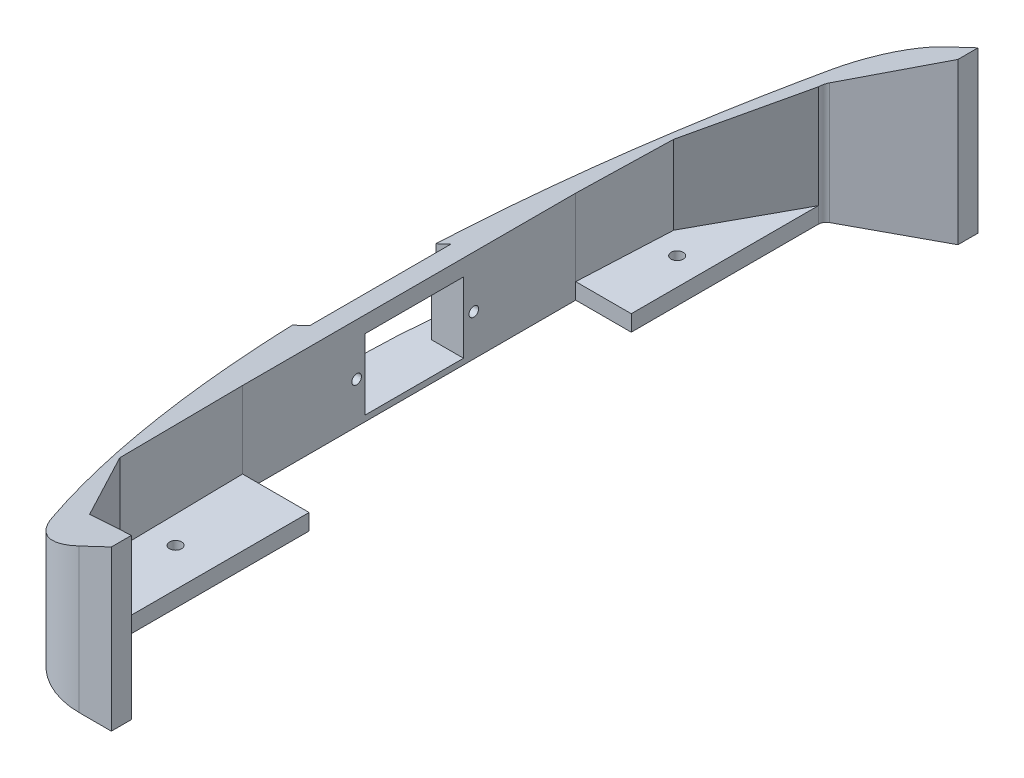
SolidWorks part; units mm, degrees
ref_plane "Front Plane" through (0, 0, 0) normal (0, 0, 1) x (1, 0, 0)
ref_plane "Top Plane" through (0, 0, 0) normal (0, 1, 0) x (1, 0, 0)
ref_plane "Right Plane" through (0, 0, 0) normal (1, 0, 0) x (0, 0, -1)
sketch "front_sketch" plane through (0, 0, 0) normal (0, 1, 0) x (1, 0, 0)
  line L4 (-94.9614, 124.4785) -> (-121.3453, 110.2345)
  line L10 (-122.6787, 107.9994) -> (-122.6787, 48.8108)
  line L24 (-94.9614, 130.8285) -> (-94.9614, 124.4785) construction
  line L25 (-94.9614, 124.4785) -> (-69.5614, 124.4785) construction
  line L28 (-95.6016, -142.8102) -> (-95.6016, -136.4602)
  line L29 (-95.6016, -136.4602) -> (-70.2016, -136.4602) construction
  line L34 (-122.6787, 48.8108) -> (-140.2508, 48.8108)
  line L36 (-140.2508, 48.8108) -> (-140.2508, -56.6452)
  line L43 (-140.2508, -56.6452) -> (-119.167, -56.6452)
  line L44 (-119.167, -56.6452) -> (-119.167, -126.1123)
  line L50 (-119.167, -126.1123) -> (-95.6016, -136.4602)
  line L129 (-94.9614, 130.8285) -> (-69.5614, 130.8285) construction
  line L130 (-94.9614, 130.8285) -> (-69.5614, 130.8285) construction
  line L225 (-95.5505, 130.8285) -> (-157.7358, 130.8285) construction
  line L248 (-94.9614, 130.8285) -> (-95.5505, 130.8285) construction
  line L254 (-94.9614, 130.8285) -> (-95.5505, 130.8285) construction
  line L257 (-94.9614, 130.8285) -> (-105.2412, 130.8285)
  line L258 (-95.5505, 130.8285) -> (-94.9614, 130.8285) construction
  line L259 (-95.6016, -142.8102) -> (-105.7982, -142.8102)
  line L260 (-94.9614, 124.4785) -> (-94.9614, 130.8285)
  line L261 (-94.9614, 130.8285) -> (-95.5505, 130.8285) construction
  line L263 (-95.6016, -142.8102) -> (-70.2016, -142.8102) construction
  line L264 (-95.6016, -142.8102) -> (-70.2016, -142.8102) construction
  line L267 (-97.1554, -142.8102) -> (-95.6016, -142.8102) construction
  line L294 (-94.9614, 130.8285) -> (-95.5505, 130.8285) construction
  line L295 (-157.7358, 130.8285) -> (-157.7358, -142.8102) construction
  line L296 (-157.7358, -142.8102) -> (-97.1554, -142.8102) construction
  line L297 (-95.5505, 130.8285) -> (-157.7358, 130.8285) construction
  arc A41 (-127.9188, 116.8691) -> (-128.5327, -128.7374) centre (116.7138, -6.5464) ccw
  arc A42 (-127.9188, 116.8691) -> (-105.2412, 130.8285) centre (-105.2412, 105.4285) cw
  arc A43 (-128.5327, -128.7374) -> (-105.7982, -142.8102) centre (-105.7982, -117.4102) ccw
  circle A44 centre (-131.2964, 71.9636) radius 1.905
  circle A45 centre (-131.2964, -86.7864) radius 1.905
  arc A48 (-122.6787, 107.9994) -> (-121.3453, 110.2345) centre (-120.1387, 107.9994) cw
  dimension "D12" = 25.4
  dimension "D14" = 25.4
  dimension "D30" = 3.81
  dimension "D4" = 2.54
  dimension "D19" = 6.35
  dimension "D27" = 10.2799
  dimension "D28" = 10.1966
extrude "Boss-Extrude1" add sketch "front_sketch" along normal blind 50.8
sketch "Sketch1" plane through (0, 50.8, 0) normal (0, 1, 0) x (1, 0, 0)
  line L0 (-122.6787, 48.8108) -> (-122.6787, 107.9994)
  line L1 (-122.6787, 107.9994) -> (-138.8333, 78.4051)
  line L2 (-138.8333, 78.4051) -> (-140.2508, 48.8108)
  line L3 (-140.2508, 48.8108) -> (-122.6787, 48.8108)
  line L4 (-119.167, -56.6452) -> (-140.2508, -56.6452)
  line L5 (-119.167, -56.6452) -> (-140.2508, -56.6452) construction
  line L6 (-140.2508, -56.6452) -> (-140.2508, 48.8108) construction
  line L7 (-140.2508, -56.6452) -> (-139.5421, -96.1925)
  line L8 (-139.5421, -96.1925) -> (-119.167, -126.1123)
  line L9 (-119.167, -126.1123) -> (-119.167, -56.6452) construction
  line L10 (-95.6016, -136.4602) -> (-119.167, -126.1123) construction
  line L11 (-119.167, -126.1123) -> (-119.167, -56.6452)
extrude "Cut-Extrude1" cut sketch "Sketch1" against normal blind 45.72
sketch "Sketch3" plane through (0, 0, 142.8102) normal (0, 0, 1) x (1, 0, 0)
  line L0 (-94.9614, 50.8) -> (-157.2871, 21.2708)
  line L1 (-157.2871, 50.8) -> (-157.2871, 0) construction
  line L2 (-157.2871, 21.2708) -> (-157.2871, 50.8)
  line L3 (-157.2871, 50.8) -> (-94.9614, 50.8)
extrude "Cut-Extrude2" cut sketch "Sketch3" against normal through all
sketch "Sketch4" plane through (-140.2508, 0, 0) normal (1, 0, 0) x (0, 0, -1)
  line L0 (-24.4046, 24.1445) -> (20.2563, 24.1445)
  line L1 (-24.4046, 24.1445) -> (-24.4046, 5.0945)
  line L3 (20.2563, 24.1445) -> (20.2563, 5.0945)
  line L4 (-24.4046, 5.0945) -> (-24.4046, 1.8437)
  line L5 (-24.4046, 1.8437) -> (20.2563, 1.8437)
  line L6 (20.2563, 1.8437) -> (20.2563, 5.0945)
  dimension "D1" = 19.05
extrude "Cut-Extrude3" cut sketch "Sketch4" against normal through all
sketch "Sketch6" plane through (-140.2508, 0, 0) normal (1, 0, 0) x (0, 0, -1)
  line L18 (-24.4046, 24.1445) -> (-24.4046, 1.8437) construction
  line L19 (-24.4046, 24.1445) -> (-17.8803, 24.1445)
  line L20 (-24.4046, 24.1445) -> (-24.4046, 1.8437)
  line L21 (-24.4046, 1.8437) -> (-17.8803, 1.8437)
  line L22 (-17.8803, 24.1445) -> (-17.8803, 1.8437)
  line L23 (-24.4046, 1.8437) -> (20.2563, 1.8437) construction
  line L24 (20.2563, 24.1445) -> (-24.4046, 24.1445) construction
  line L25 (20.2563, 1.8437) -> (13.2935, 1.8437)
  line L26 (20.2563, 1.8437) -> (20.2563, 24.1445)
  line L27 (20.2563, 24.1445) -> (13.2935, 24.1445)
  line L28 (13.2935, 1.8437) -> (13.2935, 24.1445)
  circle A1 centre (16.554, 12.9915) radius 1.524
  circle A2 centre (-20.53, 12.9915) radius 1.524
extrude "Boss-Extrude2" add sketch "Sketch6" against normal blind 10.16
